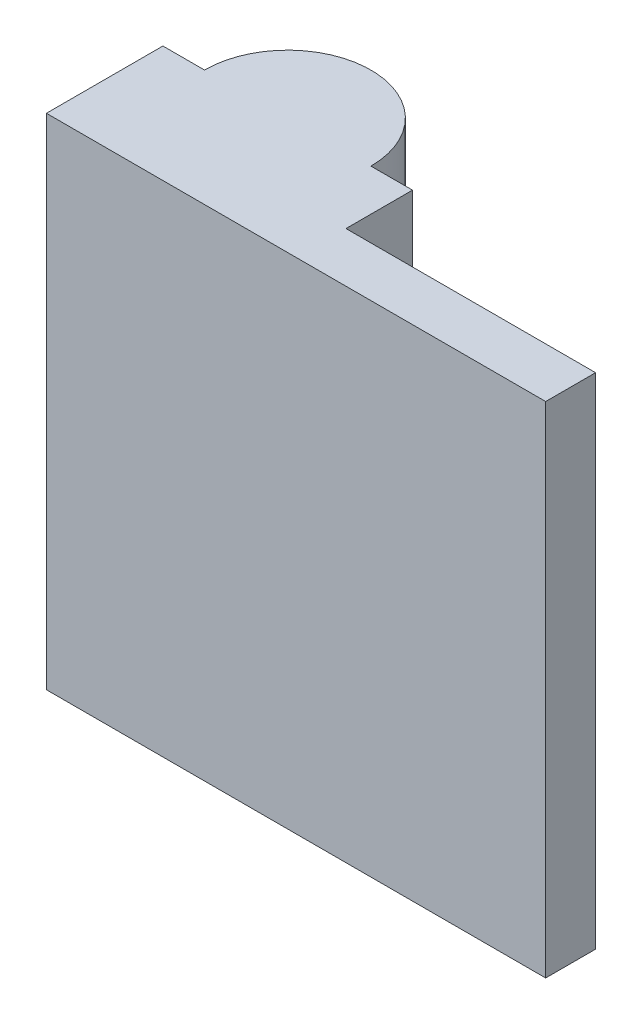
SolidWorks part; units mm, degrees
ref_plane "Front Plane" through (0, 0, 0) normal (0, 0, 1) x (1, 0, 0)
ref_plane "Top Plane" through (0, 0, 0) normal (0, 1, 0) x (1, 0, 0)
ref_plane "Right Plane" through (0, 0, 0) normal (1, 0, 0) x (0, 0, -1)
sketch "Sketch1" plane through (0, 0, 0) normal (0, 0, 1) x (1, 0, 0)
  line L1 (0, 0) -> (30, 0)
  line L2 (0, 0) -> (0, 30)
  line L3 (0, 30) -> (30, 30)
  line L4 (30, 0) -> (30, 30)
  dimension "D1" = 30
  dimension "D2" = 30
extrude "Boss-Extrude1" add sketch "Sketch1" along normal blind 10
sketch "Sketch2" plane through (0, 0, 0) normal (0, 0, -1) x (-1, 0, 0)
  line L0 (-30, 30) -> (0, 30) construction
  line L1 (-30, 0) -> (-15, 0)
  line L2 (-30, 0) -> (-30, 30)
  line L3 (-30, 30) -> (-15, 30)
  line L4 (-15, 0) -> (-15, 30)
  line L5 (0, 0) -> (-30, 0) construction
  dimension "D1" = 15
extrude "Cut-Extrude1" cut sketch "Sketch2" against normal blind 4
sketch "Sketch4" plane through (0, 0, 4) normal (0, 0, -1) x (-1, 0, 0)
  line L0 (-30, 15) -> (-21.2468, 15) construction
  line L1 (-30, 30) -> (-30, 0) construction
  line L2 (-30, 0) -> (-15, 0) construction
  circle A0 centre (-22.5, 0) radius 1.75
  circle A1 centre (-22.5, 30) radius 1.75
  point P10 (-22.5, 0)
  dimension "D2" = 3.5
  dimension "D1" = 30
extrude "Cut-Extrude3" cut sketch "Sketch4" against normal blind 30
sketch "Sketch7" plane through (0, 0, 0) normal (0, -1, 0) x (1, 0, 0)
  line L0 (0, 0) -> (15, 0) construction
  circle A0 centre (7.5, 0) radius 5
  dimension "D1" = 10
extrude "Boss-Extrude2" add sketch "Sketch7" against normal blind 40
sketch "Sketch8" plane through (0, 0, 0) normal (0, -1, 0) x (1, 0, 0)
  circle A0 centre (7.5, 0) radius 3.5
  dimension "D1" = 7
extrude "Cut-Extrude4" cut sketch "Sketch8" against normal blind 30
sketch "Sketch9" plane through (0, 0, 0) normal (-1, 0, 0) x (0, 0, 1)
  line L0 (10, 30) -> (0, 30) construction
  line L1 (10, 0) -> (7, 0)
  line L2 (10, 0) -> (10, 30)
  line L3 (10, 30) -> (7, 30)
  line L4 (7, 0) -> (7, 30)
  line L5 (10, 30) -> (10, 0) construction
  line L6 (10, 0) -> (0, 0) construction
  dimension "D1" = 3
extrude "Cut-Extrude5" cut sketch "Sketch9" against normal through all
sketch "Sketch11" plane through (0, 0, 0) normal (0, 0, -1) x (-1, 0, 0)
  line L0 (-2.5, 30) -> (0, 30) construction
  line L1 (1.0688, 30) -> (-32.102, 30)
  line L2 (1.0688, 30) -> (1.0688, 43.1096)
  line L3 (1.0688, 43.1096) -> (-32.102, 43.1096)
  line L4 (-32.102, 30) -> (-32.102, 43.1096)
extrude "Cut-Extrude6" cut sketch "Sketch11" against normal through all and the other way through all
sketch "Sketch12" plane through (0, 30, 0) normal (0, 1, 0) x (1, 0, 0)
  circle A0 centre (7.5, 0) radius 3.5
extrude "Boss-Extrude3" add sketch "Sketch12" against normal blind 10
sketch "Sketch13" plane through (0, 0, 4) normal (0, 0, -1) x (-1, 0, 0)
  line L0 (-24.25, 30) -> (-20.75, 30)
  line L1 (-30, 15) -> (-24.25, 15) construction
  line L2 (-30, 30) -> (-30, 0) construction
  line L3 (-24.25, 0) -> (-20.75, 0)
  arc A0 (-24.25, 30) -> (-20.75, 30) centre (-22.5, 30) ccw
  arc A1 (-24.25, 30) -> (-20.75, 30) centre (-22.5, 30) ccw construction
  arc A2 (-24.25, 0) -> (-20.75, 0) centre (-22.5, 0) cw
extrude "Boss-Extrude4" add sketch "Sketch13" against normal blind 3
